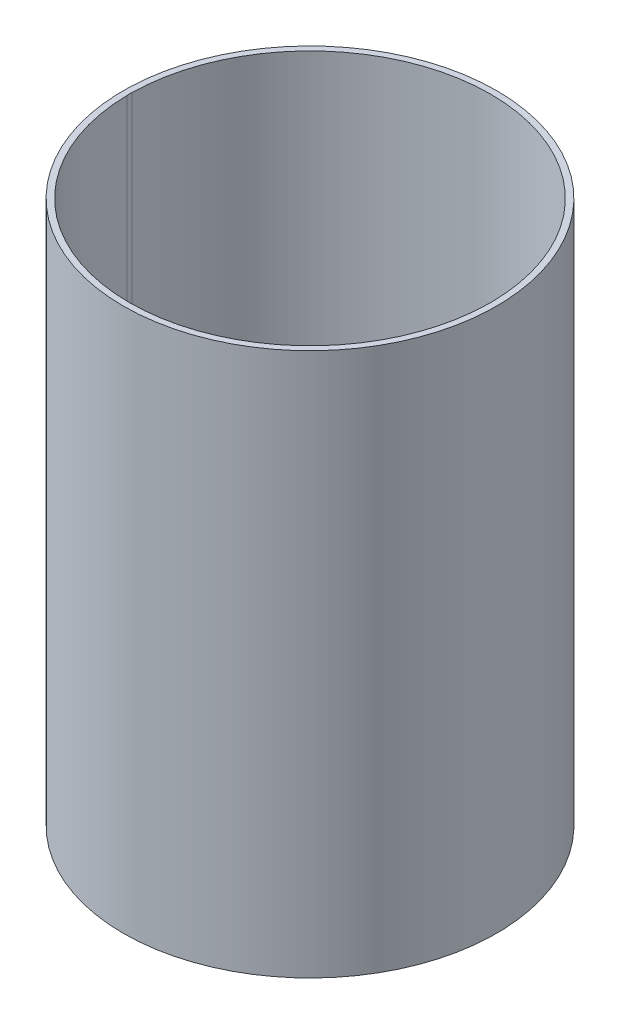
SolidWorks part; units mm, degrees
ref_plane "Front Plane" through (0, 0, 0) normal (0, 0, 1) x (1, 0, 0)
ref_plane "Top Plane" through (0, 0, 0) normal (0, 1, 0) x (1, 0, 0)
ref_plane "Right Plane" through (0, 0, 0) normal (1, 0, 0) x (0, 0, -1)
sketch "Sketch1" plane through (0, 0, 0) normal (0, 1, 0) x (1, 0, 0)
  circle A0 centre (0, 0) radius 92.71
  circle A1 centre (0, 0) radius 53.975
  dimension "D1" = 185.42
  dimension "D2" = 107.95
extrude "Boss-Extrude1" add sketch "Sketch1" along normal blind 3.175
sketch "Sketch2" plane through (0, 3.175, 0) normal (0, 1, 0) x (1, 0, 0)
  circle A0 centre (0, 0) radius 92.71
  circle A1 centre (0, 0) radius 89.71
  circle A2 centre (0, 0) radius 92.71 construction
  dimension "D1" = 3
extrude "Boss-Extrude2" add sketch "Sketch2" along normal blind 266.7
sketch "Sketch3" plane through (0, 0, 0) normal (0, -1, 0) x (1, 0, 0)
  line L0 (0, 0) -> (-80.264, 0) construction
  line L1 (0, 0) -> (0, 76.902) construction
  circle A0 centre (-80.264, 0) radius 9.525
  circle A1 centre (80.264, 0) radius 9.525
  dimension "D1" = 80.264
  dimension "D2" = 19.05
extrude "Cut-Extrude1" cut sketch "Sketch3" against normal through all
